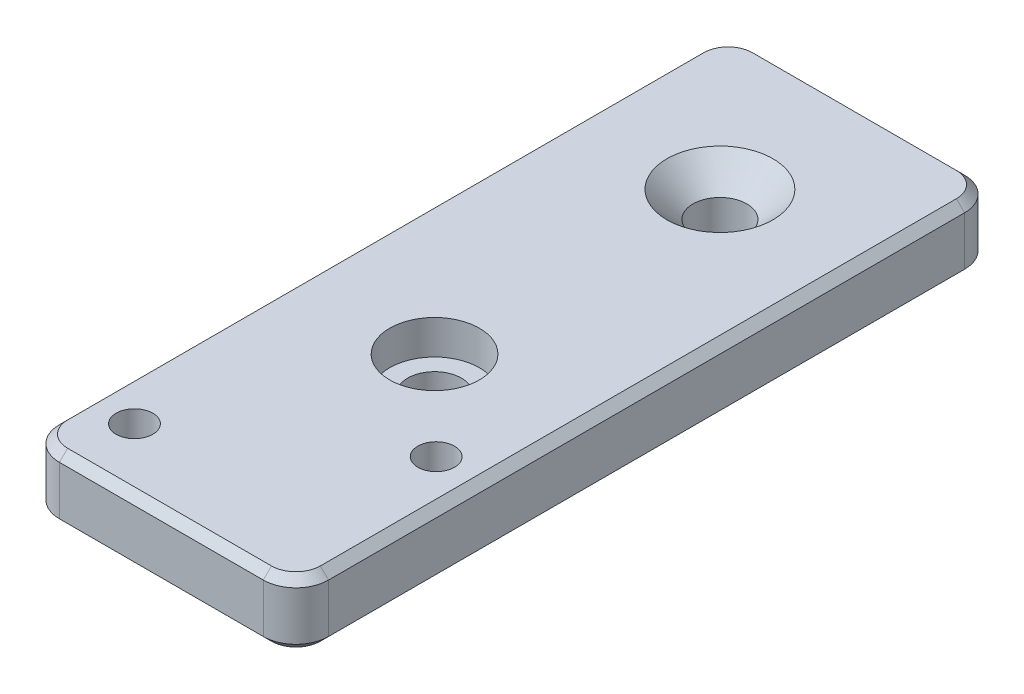
SolidWorks part; units mm, degrees
ref_plane "Front Plane" through (0, 0, 0) normal (0, 0, 1) x (1, 0, 0)
ref_plane "Top Plane" through (0, 0, 0) normal (0, 1, 0) x (1, 0, 0)
ref_plane "Right Plane" through (0, 0, 0) normal (1, 0, 0) x (0, 0, -1)
sketch "Sketch1" plane through (0, 0, 0) normal (0, 1, 0) x (1, 0, 0)
  line L1 (-16.5, 43) -> (16.5, 43)
  line L2 (-16.5, 43) -> (-16.5, -43)
  line L3 (-16.5, -43) -> (16.5, -43)
  line L4 (16.5, 43) -> (16.5, -43)
  line L5 (-16.5, 43) -> (16.5, -43) construction
  line L6 (-16.5, -43) -> (16.5, 43) construction
  point P0 (0, 0)
  dimension "D1" = 86
  dimension "D2" = 33
extrude "Boss-Extrude1" add sketch "Sketch1" along normal blind 8
fillet "Fillet1" radius 4 4 edges at (-16.5, 4, -43) (16.5, 4, -43) (-16.5, 4, 43) (16.5, 4, 43)
chamfer "Chamfer1" distance 1 angle 45 16 edges at (16.5, 8, 0) (15.3284, 8, 41.8284) (0, 8, 43) (-15.3284, 8, 41.8284) (-16.5, 8, 0) (-15.3284, 8, -41.8284) (0, 8, -43) (15.3284, 8, -41.8284) (0, 0, 43) (-15.3284, 0, 41.8284) (15.3284, 0, 41.8284) (16.5, 0, 0) (15.3284, 0, -41.8284) (-16.5, 0, 0) (-15.3284, 0, -41.8284) (0, 0, -43)
sketch "Sketch2" plane through (0, 8, 0) normal (0, 1, 0) x (1, 0, 0)
  line L0 (-12.5, 43) -> (12.5, 43) construction
  line L1 (12.5, -43) -> (-12.5, -43) construction
  line L2 (-16.5, -39) -> (-16.5, 39) construction
  line L3 (16.5, 39) -> (16.5, -39) construction
  circle A0 centre (0, 25.5) radius 3.3
  circle A1 centre (0, -9.5) radius 3.3
  circle A2 centre (11, -20.3) radius 2.25
  circle A3 centre (-11, -35.3) radius 2.25
  dimension "D1" = 17.5
  dimension "D3" = 7.7
  dimension "D2" = 35
  dimension "D4" = 15
  dimension "D5" = 5.5
  dimension "D6" = 5.5
extrude "Cut-Extrude1" cut sketch "Sketch2" against normal blind 8
sketch "Sketch3" plane through (0, 8, 0) normal (0, 1, 0) x (1, 0, 0)
  circle A0 centre (0, -9.5) radius 5.5
extrude "Cut-Extrude2" cut sketch "Sketch3" against normal blind 4.2
chamfer "Chamfer3" distance 3.2 angle 45 1 edges at (0, 8, -22.2)
sketch "Sketch4" plane through (0, 0, 0) normal (0, -1, 0) x (1, 0, 0)
  circle A0 centre (11, 20.3) radius 4
  circle A1 centre (-11, 35.3) radius 4
extrude "Cut-Extrude3" cut sketch "Sketch4" against normal blind 4.4
